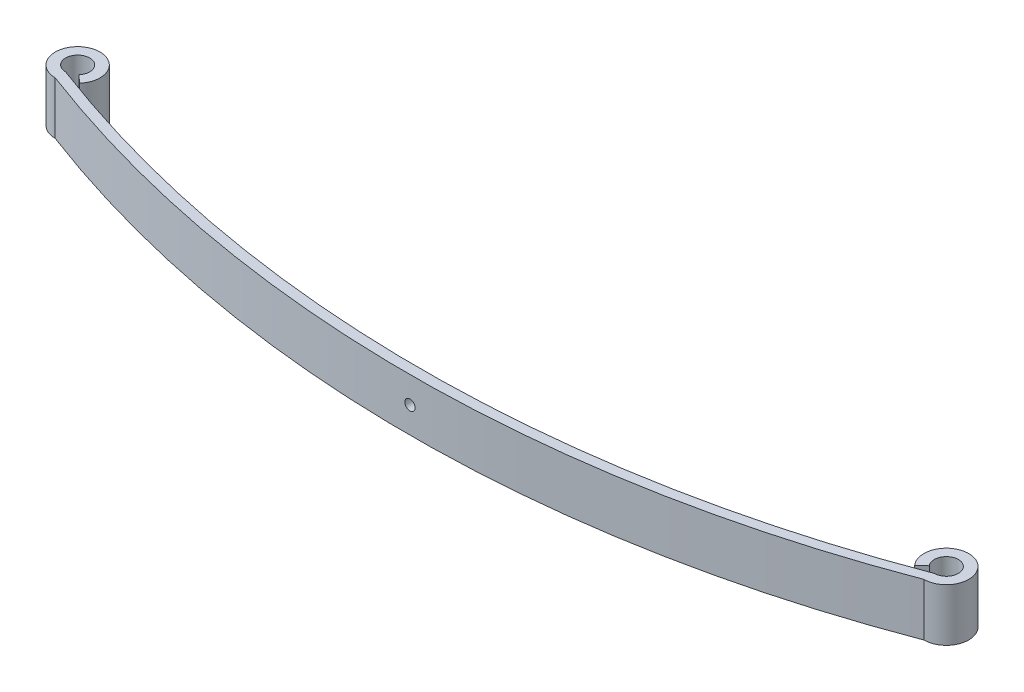
SolidWorks part; units mm, degrees
ref_plane "Front Plane" through (0, 0, 0) normal (0, 0, 1) x (1, 0, 0)
ref_plane "Top Plane" through (0, 0, 0) normal (0, 1, 0) x (1, 0, 0)
ref_plane "Right Plane" through (0, 0, 0) normal (1, 0, 0) x (0, 0, -1)
sketch "Sketch1" plane through (0, 0, 0) normal (0, 1, 0) x (1, 0, 0)
  line L0 (-630, 0) -> (630, 0) construction
  line L1 (-210.8013, -133) -> (245.5549, -133) construction
  line L2 (0, 0) -> (0, -133) construction
  line L4 (-616.835, -11.5296) -> (-605.5506, -21.4121)
  line L5 (616.835, -11.5296) -> (605.5506, -21.4121)
  arc A0 (-616.835, -11.5296) -> (-630, -17.5) centre (-630, 0) ccw
  arc A1 (630, -17.5) -> (616.835, -11.5296) centre (630, 0) ccw
  arc A2 (-630, -17.5) -> (630, -17.5) centre (0, 1642.9318) ccw
  arc A3 (-630.0011, -32.5) -> (630.0011, -32.5) centre (0, 1627.9379) ccw
  arc A4 (-605.5506, -21.4121) -> (-630.0011, -32.5) centre (-630, 0) ccw
  arc A5 (630.0011, -32.5) -> (605.5506, -21.4121) centre (630, 0) ccw
  point P10 (0, -133)
  point P13 (-630.0011, -32.5)
  point P14 (0, -148)
  point P15 (630.0011, -32.5)
  dimension "D4" = 35
  dimension "D5" = 35
  dimension "D1" = 133
  dimension "D2" = 630
  dimension "D3" = 630
  dimension "D6" = 15
  dimension "D7" = 15
  dimension "D8" = 15
extrude "Boss-Extrude3" add sketch "Sketch1" along normal blind 76.2
sketch "Sketch5" plane through (0, 0, 0) normal (0, 0, 1) x (1, 0, 0)
  circle A0 centre (0, 38.1) radius 7.5
  dimension "D2" = 15
  dimension "D1" = 38.1
extrude "Cut-Extrude3" cut sketch "Sketch5" along normal through all
